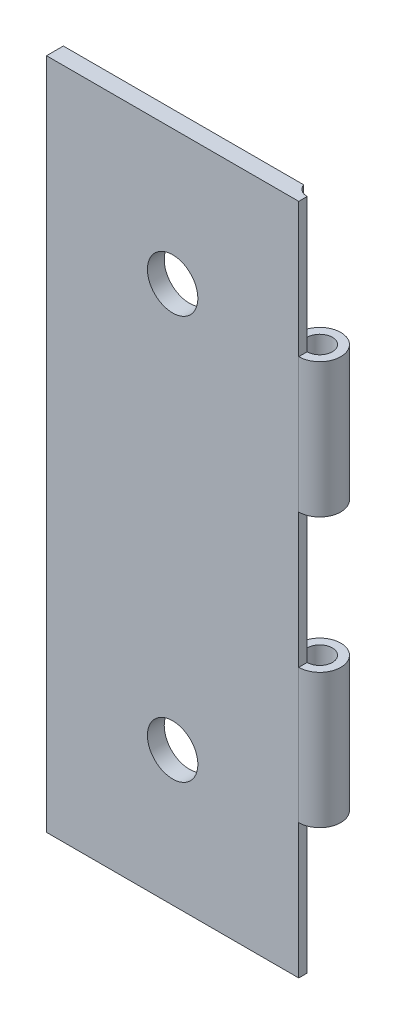
SolidWorks part; units mm, degrees
material "Stainless Steel (ferritic)"
ref_plane "Front Plane" through (0, 0, 0) normal (0, 0, 1) x (1, 0, 0)
ref_plane "Top Plane" through (0, 0, 0) normal (0, 1, 0) x (1, 0, 0)
ref_plane "Right Plane" through (0, 0, 0) normal (1, 0, 0) x (0, 0, -1)
sketch "Sketch1" plane through (0, 0, 0) normal (0, 0, 1) x (1, 0, 0)
  line L0 (-7.5, 0) -> (7.5, 0) construction
  line L1 (-7.5, -20) -> (7.5, -20)
  line L2 (-7.5, -20) -> (-7.5, 20)
  line L3 (-7.5, 20) -> (7.5, 20)
  line L4 (7.5, -20) -> (7.5, 20)
  line L5 (-7.5, -20) -> (7.5, 20) construction
  line L6 (-7.5, 20) -> (7.5, -20) construction
  circle A0 centre (0, 12) radius 1.5
  circle A1 centre (0, -12) radius 1.5
  point P0 (0, 0)
  dimension "D3" = 3
  dimension "D1" = 15
  dimension "D2" = 40
  dimension "D4" = 8
extrude "Boss-Extrude2" add sketch "Sketch1" along normal blind 1
sketch "Sketch5" plane through (0, 20, 0) normal (0, 1, 0) x (1, 0, 0)
  line L0 (7.5, -1) -> (-7.5, -1) construction
  line L1 (7.5, -1) -> (7.5, 0) construction
  circle A0 centre (7.5, 0.25) radius 1.25
  circle A1 centre (7.5, 0.25) radius 0.75
  line M3 (7.5, 0) -> (-7.5, 0)
  line M6 (7.5, -1) -> (7.5, 0)
  dimension "D1" = 2.5
  dimension "D4" = 1.5
  dimension "D2" = 1.25
  dimension "D3" = 0
extrude "Boss-Extrude5" add sketch "Sketch5" against normal blind 8 from offset 8 contours A1 A0 M6 M3 offset against normal yes
pattern_linear "LPattern2" count 2 spacing 16 along (0, -1, 0) of "Boss-Extrude5"
sketch "Sketch6" plane through (0, 20, 0) normal (0, 1, 0) x (1, 0, 0)
  circle A0 centre (7.5, 0.25) radius 0.75
  dimension "D1" = 1.5
extrude "Cut-Extrude3" cut sketch "Sketch6" against normal blind 40
